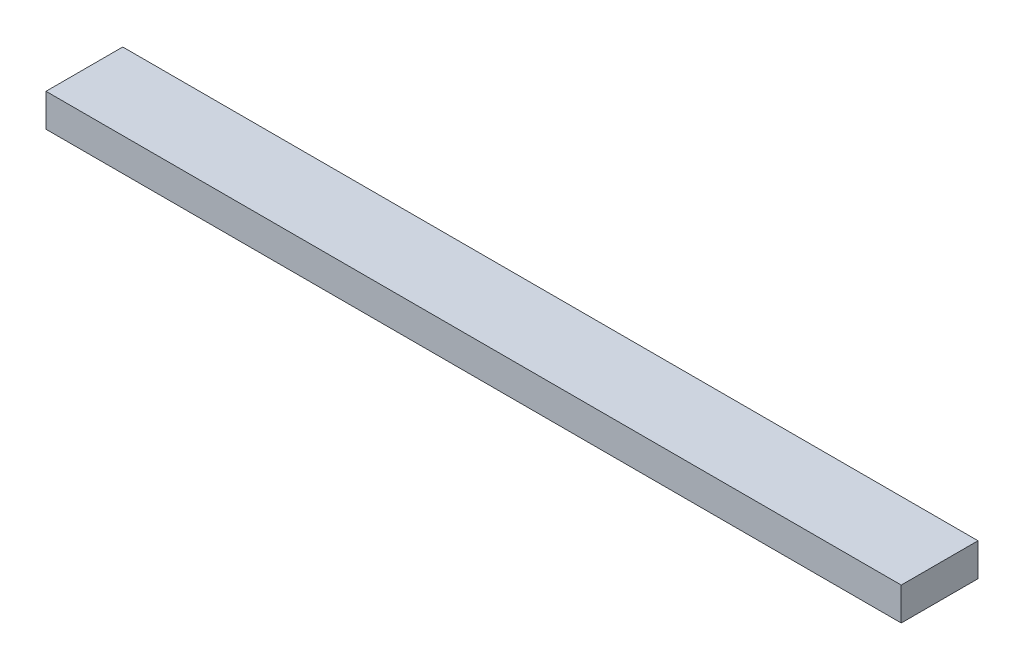
SolidWorks part; units mm, degrees
material "Pine"
ref_plane "Front Plane" through (0, 0, 0) normal (0, 0, 1) x (1, 0, 0)
ref_plane "Top Plane" through (0, 0, 0) normal (0, 1, 0) x (1, 0, 0)
ref_plane "Right Plane" through (0, 0, 0) normal (1, 0, 0) x (0, 0, -1)
sketch "Sketch1" plane through (0, 0, 0) normal (0, 1, 0) x (1, 0, 0)
  line L1 (0, 0) -> (990.6, 0)
  line L2 (0, 0) -> (0, 88.9)
  line L3 (0, 88.9) -> (990.6, 88.9)
  line L4 (990.6, 0) -> (990.6, 88.9)
  dimension "D1" = 88.9
  dimension "D2" = 990.6
extrude "Boss-Extrude1" add sketch "Sketch1" along normal blind 38.1
